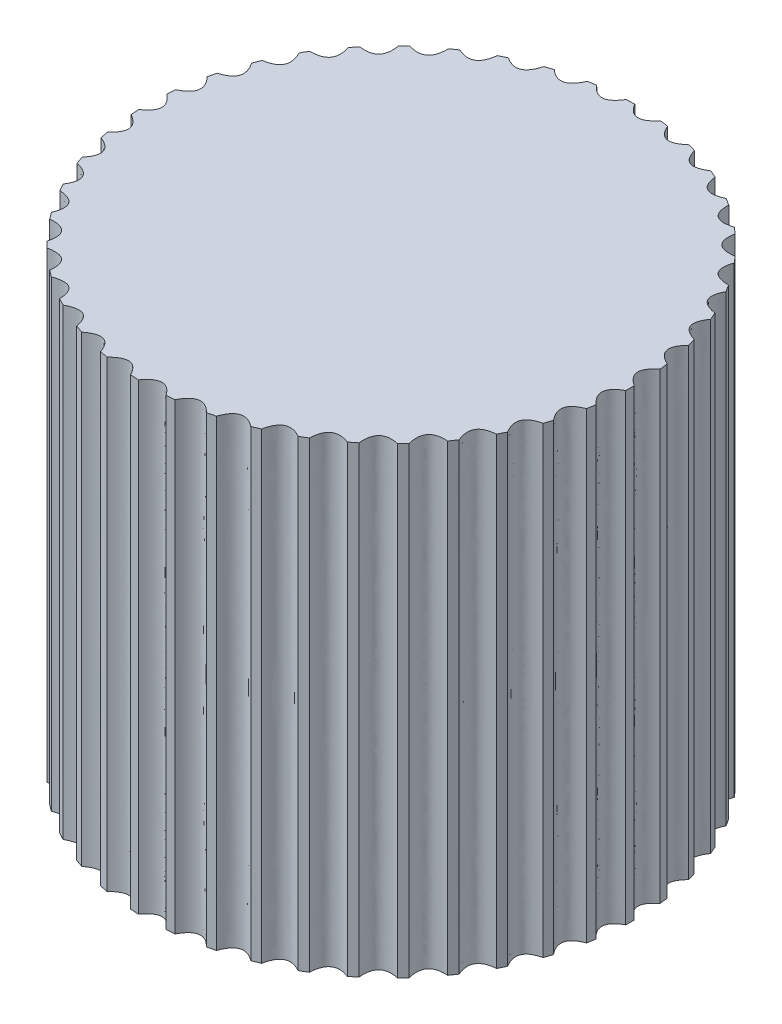
SolidWorks part; units mm, degrees
material "自定义塑料"
ref_plane "前视基准面" through (0, 0, 0) normal (0, 0, 1) x (1, 0, 0)
ref_plane "上视基准面" through (0, 0, 0) normal (0, 1, 0) x (1, 0, 0)
ref_plane "右视基准面" through (0, 0, 0) normal (1, 0, 0) x (0, 0, -1)
other "Configuration Table"
sketch "草图1" plane through (0, 0, 0) normal (0, 1, 0) x (1, 0, 0)
  spline S0 degree 2 poles (0, 10) (0.4899, 9.1964) (1.1197, 9.9371) knots 0 0 0 1 1 1
  spline S1 degree 2 poles (1.456, 9.8934) (1.8237, 9.027) (2.5546, 9.6682) knots 0 0 0 1 1 1
  spline S2 degree 2 poles (2.881, 9.576) (3.1186, 8.6653) (3.9351, 9.1932) knots 0 0 0 1 1 1
  spline S3 degree 2 poles (4.2446, 9.0545) (4.347, 8.1189) (5.2317, 8.5223) knots 0 0 0 1 1 1
  spline S4 degree 2 poles (5.5177, 8.34) (5.4828, 7.3994) (6.4168, 7.6697) knots 0 0 0 1 1 1
  spline S5 degree 2 poles (6.6732, 7.4477) (6.5018, 6.5223) (7.4652, 6.6537) knots 0 0 0 1 1 1
  spline S6 degree 2 poles (7.6865, 6.3967) (7.3821, 5.5061) (8.3544, 5.4958) knots 0 0 0 1 1 1
  spline S7 degree 2 poles (8.5359, 5.2094) (8.1052, 4.3726) (9.0656, 4.2209) knots 0 0 0 1 1 1
  spline S8 degree 2 poles (9.2035, 3.911) (8.6554, 3.1459) (9.5835, 2.8559) knots 0 0 0 1 1 1
  spline S9 degree 2 poles (9.6748, 2.5293) (9.0212, 1.8521) (9.8972, 1.4301) knots 0 0 0 1 1 1
  spline S10 degree 2 poles (9.94, 1.0937) (9.1948, 0.5189) (10, -0.0262) knots 0 0 0 1 1 1
  spline S11 degree 2 poles (9.9933, -0.3652) (9.1723, -0.8254) (9.8896, -1.4819) knots 0 0 0 1 1 1
  spline S12 degree 2 poles (9.8337, -1.8164) (8.9544, -2.1522) (9.5684, -2.906) knots 0 0 0 1 1 1
  spline S13 degree 2 poles (9.4644, -3.2288) (8.5456, -3.433) (9.0433, -4.2682) knots 0 0 0 1 1 1
  spline S14 degree 2 poles (8.8934, -4.5724) (7.9547, -4.6407) (8.3255, -5.5395) knots 0 0 0 1 1 1
  spline S15 degree 2 poles (8.1329, -5.8186) (7.1943, -5.7494) (7.4302, -6.6927) knots 0 0 0 1 1 1
  spline S16 degree 2 poles (7.199, -6.9407) (6.2805, -6.7356) (6.3766, -7.7032) knots 0 0 0 1 1 1
  spline S17 degree 2 poles (6.1117, -7.915) (5.2328, -7.5783) (5.187, -8.5495) knots 0 0 0 1 1 1
  spline S18 degree 2 poles (4.8942, -8.7205) (4.0736, -8.2595) (3.8869, -9.2137) knots 0 0 0 1 1 1
  spline S19 degree 2 poles (3.5723, -9.3402) (2.8276, -8.7646) (2.504, -9.6814) knots 0 0 0 1 1 1
  spline S20 degree 2 poles (2.1743, -9.7608) (1.5214, -9.0829) (1.0677, -9.9428) knots 0 0 0 1 1 1
  spline S21 degree 2 poles (0.73, -9.9733) (0.1827, -9.2076) (-0.3914, -9.9923) knots 0 0 0 1 1 1
  spline S22 degree 2 poles (-0.73, -9.9733) (-1.1599, -9.1361) (-1.8421, -9.8289) knots 0 0 0 1 1 1
  spline S23 degree 2 poles (-2.1743, -9.7608) (-2.4778, -8.8698) (-3.2536, -9.4559) knots 0 0 0 1 1 1
  spline S24 degree 2 poles (-3.5723, -9.3402) (-3.7428, -8.4145) (-4.5957, -8.8814) knots 0 0 0 1 1 1
  spline S25 degree 2 poles (-4.8942, -8.7205) (-4.9281, -7.7799) (-5.8399, -8.1176) knots 0 0 0 1 1 1
  spline S26 degree 2 poles (-6.1117, -7.915) (-6.0083, -6.9795) (-6.9596, -7.1808) knots 0 0 0 1 1 1
  spline S27 degree 2 poles (-7.199, -6.9407) (-6.9605, -6.0303) (-7.9309, -6.091) knots 0 0 0 1 1 1
  spline S28 degree 2 poles (-8.1329, -5.8186) (-7.7644, -4.9526) (-8.7333, -4.8713) knots 0 0 0 1 1 1
  spline S29 degree 2 poles (-8.8934, -4.5724) (-8.4027, -3.7693) (-9.3495, -3.5479) knots 0 0 0 1 1 1
  spline S30 degree 2 poles (-9.4644, -3.2288) (-8.862, -2.5057) (-9.7664, -2.1487) knots 0 0 0 1 1 1
  spline S31 degree 2 poles (-9.8337, -1.8164) (-9.1324, -1.1886) (-9.9752, -0.7038) knots 0 0 0 1 1 1
  spline S32 degree 2 poles (-9.9933, -0.3652) (-9.2081, 0.1537) (-9.9714, 0.7561) knots 0 0 0 1 1 1
  spline S33 degree 2 poles (-9.94, 1.0937) (-9.0876, 1.4928) (-9.755, 2.1998) knots 0 0 0 1 1 1
  spline S34 degree 2 poles (-9.6748, 2.5293) (-8.7734, 2.8) (-9.3308, 3.5967) knots 0 0 0 1 1 1
  spline S35 degree 2 poles (-9.2035, 3.911) (-8.2722, 4.0476) (-8.7077, 4.917) knots 0 0 0 1 1 1
  spline S36 degree 2 poles (-8.5359, 5.2094) (-7.5947, 5.2089) (-7.8989, 6.1324) knots 0 0 0 1 1 1
  spline S37 degree 2 poles (-7.6865, 6.3967) (-6.7554, 6.2592) (-6.9219, 7.2172) knots 0 0 0 1 1 1
  spline S38 degree 2 poles (-6.6732, 7.4477) (-5.772, 7.1761) (-5.7973, 8.1481) knots 0 0 0 1 1 1
  spline S39 degree 2 poles (-5.5177, 8.34) (-4.6657, 7.9401) (-4.5491, 8.9054) knots 0 0 0 1 1 1
  spline S40 degree 2 poles (-4.2446, 9.0545) (-3.4599, 8.5348) (-3.204, 9.4728) knots 0 0 0 1 1 1
  spline S41 degree 2 poles (-2.881, 9.576) (-2.1803, 8.9476) (-1.7906, 9.8384) knots 0 0 0 1 1 1
  spline S42 degree 2 poles (-1.456, 9.8934) (-0.8543, 9.1697) (-0.3391, 9.9943) knots 0 0 0 1 1 1
  spline S43 degree 2 poles (-8.7077, 4.917) (-8.6594, 5.0823) (-8.5359, 5.2094) knots 0 0 0 1 1 1
  spline S44 degree 1 poles (-9.2035, 3.911) (-9.3308, 3.5967) knots 0 0 1 1
  spline S45 degree 1 poles (-9.6748, 2.5293) (-9.755, 2.1998) knots 0 0 1 1
  spline S46 degree 1 poles (-9.94, 1.0937) (-9.9714, 0.7561) knots 0 0 1 1
  spline S47 degree 1 poles (-9.9933, -0.3652) (-9.9752, -0.7038) knots 0 0 1 1
  spline S48 degree 1 poles (-9.8337, -1.8164) (-9.7664, -2.1487) knots 0 0 1 1
  spline S49 degree 1 poles (-9.4644, -3.2288) (-9.3495, -3.5479) knots 0 0 1 1
  spline S50 degree 1 poles (-8.8934, -4.5724) (-8.7333, -4.8713) knots 0 0 1 1
  spline S51 degree 1 poles (-8.1329, -5.8186) (-7.9309, -6.091) knots 0 0 1 1
  spline S52 degree 1 poles (-7.199, -6.9407) (-6.9596, -7.1808) knots 0 0 1 1
  spline S53 degree 1 poles (-6.1117, -7.915) (-5.8399, -8.1176) knots 0 0 1 1
  spline S54 degree 1 poles (-4.8942, -8.7205) (-4.5957, -8.8814) knots 0 0 1 1
  spline S55 degree 1 poles (-3.5723, -9.3402) (-3.2536, -9.4559) knots 0 0 1 1
  spline S56 degree 1 poles (-2.1743, -9.7608) (-1.8421, -9.8289) knots 0 0 1 1
  spline S57 degree 1 poles (-0.73, -9.9733) (-0.3914, -9.9923) knots 0 0 1 1
  spline S58 degree 1 poles (0.73, -9.9733) (1.0677, -9.9428) knots 0 0 1 1
  spline S59 degree 1 poles (2.1743, -9.7608) (2.504, -9.6814) knots 0 0 1 1
  spline S60 degree 1 poles (3.5723, -9.3402) (3.8869, -9.2137) knots 0 0 1 1
  spline S61 degree 1 poles (4.8942, -8.7205) (5.187, -8.5495) knots 0 0 1 1
  spline S62 degree 1 poles (6.1117, -7.915) (6.3766, -7.7032) knots 0 0 1 1
  spline S63 degree 1 poles (7.199, -6.9407) (7.4302, -6.6927) knots 0 0 1 1
  spline S64 degree 1 poles (8.1329, -5.8186) (8.3255, -5.5395) knots 0 0 1 1
  spline S65 degree 1 poles (8.8934, -4.5724) (9.0433, -4.2682) knots 0 0 1 1
  spline S66 degree 1 poles (9.4644, -3.2288) (9.5684, -2.906) knots 0 0 1 1
  spline S67 degree 1 poles (9.8896, -1.4819) (9.8337, -1.8164) knots 0 0 1 1
  spline S68 degree 1 poles (10, -0.0262) (9.9933, -0.3652) knots 0 0 1 1
  spline S69 degree 1 poles (9.8972, 1.4301) (9.94, 1.0937) knots 0 0 1 1
  spline S70 degree 1 poles (9.5835, 2.8559) (9.6748, 2.5293) knots 0 0 1 1
  spline S71 degree 1 poles (9.0656, 4.2209) (9.2035, 3.911) knots 0 0 1 1
  spline S72 degree 1 poles (8.3544, 5.4958) (8.5359, 5.2094) knots 0 0 1 1
  spline S73 degree 1 poles (7.4652, 6.6537) (7.6865, 6.3967) knots 0 0 1 1
  spline S74 degree 1 poles (6.4168, 7.6697) (6.6732, 7.4477) knots 0 0 1 1
  spline S75 degree 1 poles (5.2317, 8.5223) (5.5177, 8.34) knots 0 0 1 1
  spline S76 degree 1 poles (3.9351, 9.1932) (4.2446, 9.0545) knots 0 0 1 1
  spline S77 degree 1 poles (2.5546, 9.6682) (2.881, 9.576) knots 0 0 1 1
  spline S78 degree 1 poles (1.1197, 9.9371) (1.456, 9.8934) knots 0 0 1 1
  spline S79 degree 1 poles (-0.3391, 9.9943) (0, 10) knots 0 0 1 1
  spline S80 degree 1 poles (-1.7906, 9.8384) (-1.456, 9.8934) knots 0 0 1 1
  spline S81 degree 1 poles (-3.204, 9.4728) (-2.881, 9.576) knots 0 0 1 1
  spline S82 degree 1 poles (-4.5491, 8.9054) (-4.2446, 9.0545) knots 0 0 1 1
  spline S83 degree 1 poles (-5.5177, 8.34) (-5.7973, 8.1481) knots 0 0 1 1
  spline S84 degree 1 poles (-6.6732, 7.4477) (-6.9219, 7.2172) knots 0 0 1 1
  spline S85 degree 1 poles (-7.6865, 6.3967) (-7.8989, 6.1324) knots 0 0 1 1
  point P134 (0, 0)
extrude "凸台-拉伸1" add sketch "草图1" along normal blind 19
